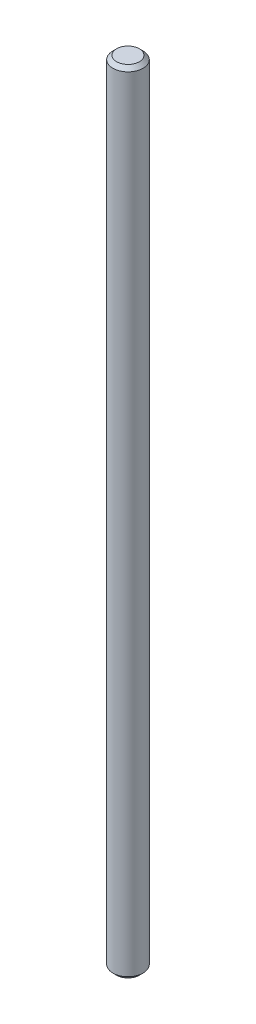
SolidWorks part; units mm, degrees
ref_plane "Front Plane" through (0, 0, 0) normal (0, 0, 1) x (1, 0, 0)
ref_plane "Top Plane" through (0, 0, 0) normal (0, 1, 0) x (1, 0, 0)
ref_plane "Right Plane" through (0, 0, 0) normal (1, 0, 0) x (0, 0, -1)
sketch "Sketch1" plane through (0, 0, 0) normal (0, 1, 0) x (1, 0, 0)
  circle A0 centre (0, 0) radius 2
  dimension "D1" = 4
extrude "Boss-Extrude1" add sketch "Sketch1" along normal blind 105
chamfer "Chamfer1" distance 0.5 angle 45 2 edges at (0, 0, 2) (0, 105, 2)
